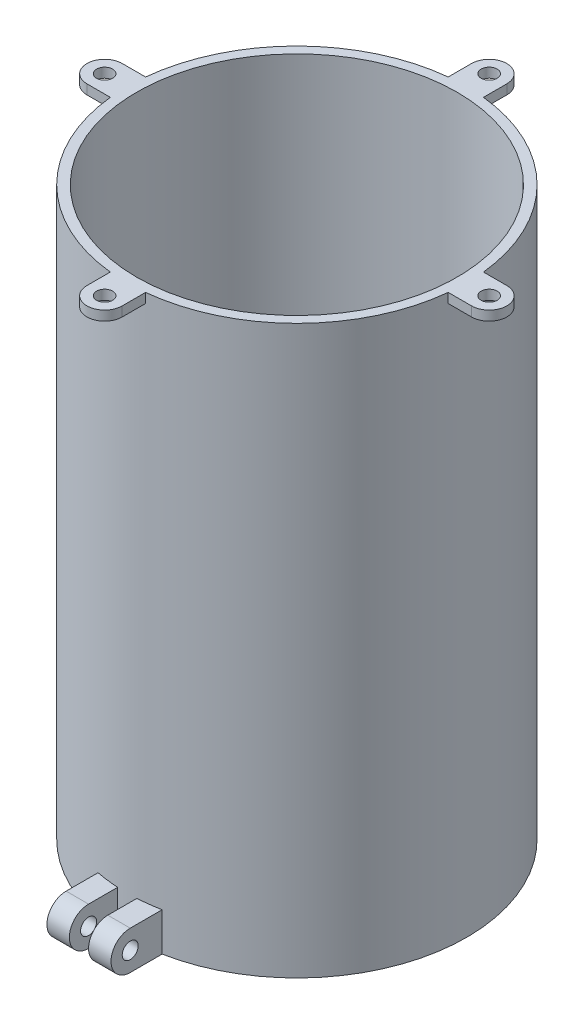
SolidWorks part; units mm, degrees
other "Marca1"
sketch "Croquis6" plane through (65.5, 0, 65.5) normal (0.0006, -0.9776, 0.2106) x (0.0216, 0.2106, 0.9773)
material "AISI 316 Chapa de acero inoxidable (SS)"
ref_plane "Alzado" through (0, 0, 0) normal (0, 0, 1) x (1, 0, 0)
ref_plane "Planta" through (0, 0, 0) normal (0, 1, 0) x (1, 0, 0)
ref_plane "Vista lateral" through (0, 0, 0) normal (1, 0, 0) x (0, 0, -1)
sketch "Croquis1" plane through (0, 0, 0) normal (0, 1, 0) x (1, 0, 0)
  circle A0 centre (0, 0) radius 50
  circle A1 centre (0, 0) radius 53
  dimension "D1" = 100
  dimension "D2" = 106
extrude "Saliente-Extruir1" add sketch "Croquis1" along normal blind 176.9
sketch "Croquis2" plane through (0, 0, 0) normal (0, -1, 0) x (1, 0, 0)
  circle A0 centre (0, 0) radius 53 construction
  circle A1 centre (0, 0) radius 53
sketch "Croquis5" plane through (0, 176.9, 0) normal (0, 1, 0) x (1, 0, 0)
  line L0 (60, 5.5) -> (52.7139, 5.5)
  line L2 (-5.5, 60) -> (-5.5, 52.7139)
  line L4 (5.5, 60) -> (5.5, 52.7139)
  line L5 (60, -5.5) -> (52.7139, -5.5)
  line L6 (5.5, -60) -> (5.5, -52.7139)
  line L7 (-5.5, -60) -> (-5.5, -52.7139)
  line L8 (-60, -5.5) -> (-52.7139, -5.5)
  line L9 (-60, 5.5) -> (-52.7139, 5.5)
  circle A1 centre (0, 0) radius 53 construction
  circle A2 centre (0, 0) radius 53
  circle A3 centre (0, 60) radius 2.5
  arc A4 (5.5, 60) -> (-5.5, 60) centre (0, 60) ccw
  circle A5 centre (0, 60) radius 5.5 construction
  arc A6 (-5.5, 59.7474) -> (5.5, 59.7474) centre (0, 0) ccw construction
  arc A7 (60, -5.5) -> (60, 5.5) centre (60, 0) ccw
  circle A8 centre (60, 0) radius 2.5
  arc A9 (-5.5, -60) -> (5.5, -60) centre (0, -60) ccw
  circle A10 centre (0, -60) radius 2.5
  arc A11 (-60, 5.5) -> (-60, -5.5) centre (-60, 0) ccw
  circle A12 centre (-60, 0) radius 2.5
  point P45 (0, 0)
  circle M3 centre (0, 0) radius 53
  dimension "D1" = 4
  dimension "D2" = 5
  dimension "D3" = 3
extrude "Saliente-Extruir4" add sketch "Croquis5" against normal blind 3 contours L9 A11 L8 A12 M3 | L4 A4 L2 A3 M3 | L5 A7 L0 A8 M3 | L7 A9 L6 A10 M3
ref_plane "Plano1" through (0, 0, 53) normal (0, 0, 1) x (1, 0, 0)
sketch "Croquis7" plane through (0, 0, 53) normal (0, 0, 1) x (1, 0, 0)
  line L0 (-53, 0) -> (53, 0) construction
  line L1 (-10, 0) -> (10, 0)
  line L2 (-10, 0) -> (-10, 12)
  line L3 (-10, 12) -> (10, 12)
  line L4 (10, 0) -> (10, 12)
  line L6 (-10, 12) -> (-3, 12)
  line L7 (-10, 12) -> (-10, 0)
  line L8 (-10, 0) -> (-3, 0)
  line L9 (-3, 12) -> (-3, 0)
  line L10 (10, 12) -> (3, 12)
  line L11 (10, 12) -> (10, 0)
  line L12 (10, 0) -> (3, 0)
  line L13 (3, 12) -> (3, 0)
  dimension "D1" = 20
  dimension "D2" = 12
  dimension "D3" = 10
  dimension "D4" = 7
  dimension "D5" = 7
extrude "Saliente-Extruir5" add sketch "Croquis7" along normal blind 15 and the other way blind 2 contours L9 L3 L2 L1 | L3 L13 L1 L4
sketch "Croquis8" plane through (-10, 0, 0) normal (-1, 0, 0) x (0, 0, 1)
  line L0 (68, 0) -> (68, 12) construction
  line L1 (68, 0) -> (68, 12) construction
  line L2 (52.0481, 0) -> (68, 0) construction
  line L3 (62, 0) -> (68, 0)
  line L4 (52.0481, 12) -> (68, 12) construction
  line L5 (62, 12) -> (68, 12)
  arc A0 (62, 0) -> (62, 12) centre (62, 6) ccw
  circle A1 centre (62, 6) radius 2.5
  line M3 (68, 12) -> (52.0481, 12)
  line M5 (52.0481, 0) -> (68, 0)
  line M6 (68, 0) -> (68, 12)
  dimension "D1" = 12
  dimension "D2" = 5
extrude "Cortar-Extruir1" cut sketch "Croquis8" against normal up to surface (20 mm away) contours A1 | A0 M6 M3 | A0 M5 M6 up to face at (10, 6, 60.024)
